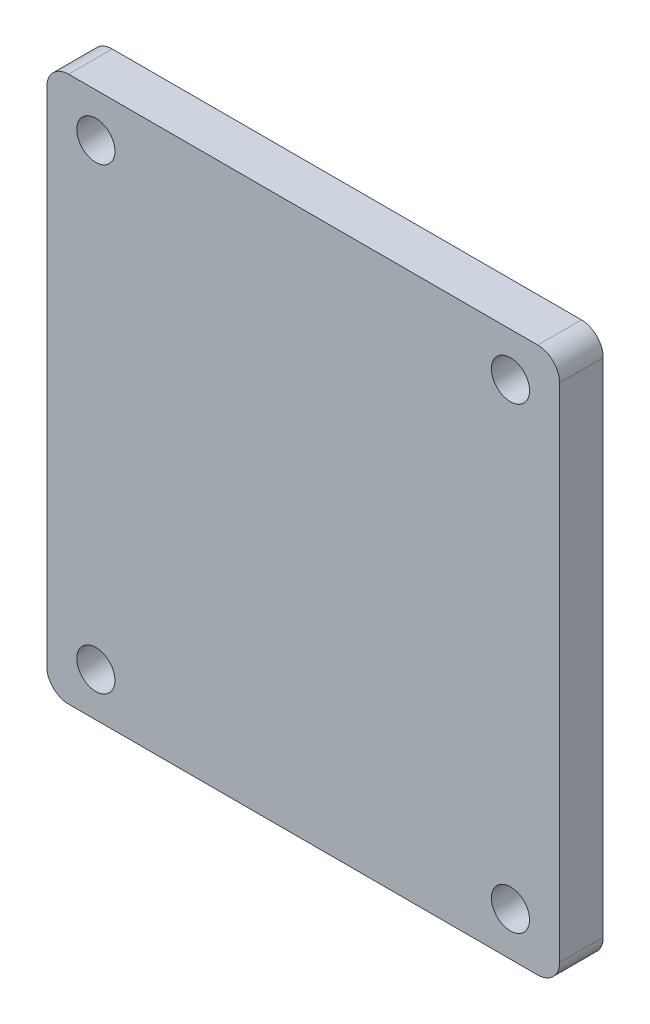
SolidWorks part; units mm, degrees
material "有机玻璃"
ref_plane "前视基准面" through (0, 0, 0) normal (0, 0, 1) x (1, 0, 0)
ref_plane "上视基准面" through (0, 0, 0) normal (0, 1, 0) x (1, 0, 0)
ref_plane "右视基准面" through (0, 0, 0) normal (1, 0, 0) x (0, 0, -1)
sketch "草图1" plane through (0, 0, 0) normal (0, 0, 1) x (1, 0, 0)
  line L1 (-23.5, -25) -> (23.5, -25)
  line L2 (-23.5, -25) -> (-23.5, 25)
  line L3 (-23.5, 25) -> (23.5, 25)
  line L4 (23.5, -25) -> (23.5, 25)
  line L5 (-23.5, -25) -> (23.5, 25) construction
  line L6 (-23.5, 25) -> (23.5, -25) construction
  point P0 (0, 0)
  dimension "D1" = 47
  dimension "D2" = 50
extrude "凸台-拉伸1" add sketch "草图1" along normal blind 4
hole_wizard "Ø3.5 (3.5) 直径孔1" positions "草图3" profile "草图2" hole size "Ø3.5" standard "GB" end condition up to next
sketch "草图3" plane through (0, 0, 4) normal (0, 0, 1) x (1, 0, 0)
  line L0 (-23.5, 0) -> (30.1005, 0) construction
  line L1 (-23.5, 25) -> (-23.5, -25) construction
  line L3 (0, 25) -> (0, -32.6862) construction
  line L4 (23.5, 25) -> (-23.5, 25) construction
  point P0 (-19, 21)
  point P2 (19, 21)
  point P4 (-19, -21)
  point P6 (19, -21)
  dimension "D1" = 42
  dimension "D2" = 38
sketch "草图2" plane through (-19, 21, 4) normal (1, 0, 0) x (0, -1, 0)
  line L0 (0, 0) -> (0, 4)
  line L1 (0, 4) -> (1.75, 4)
  line L2 (1.75, 4) -> (1.75, 0)
  line L5 (1.75, 0) -> (0, 0)
  line L11 (0, -6.35) -> (0, 107.95) construction
  dimension "通孔孔直径" = 3.5
  dimension "通孔孔深度" = 4
fillet "圆角1" radius 2 4 edges at (-23.5, 25, 2) (23.5, 25, 2) (23.5, -25, 2) (-23.5, -25, 2)
